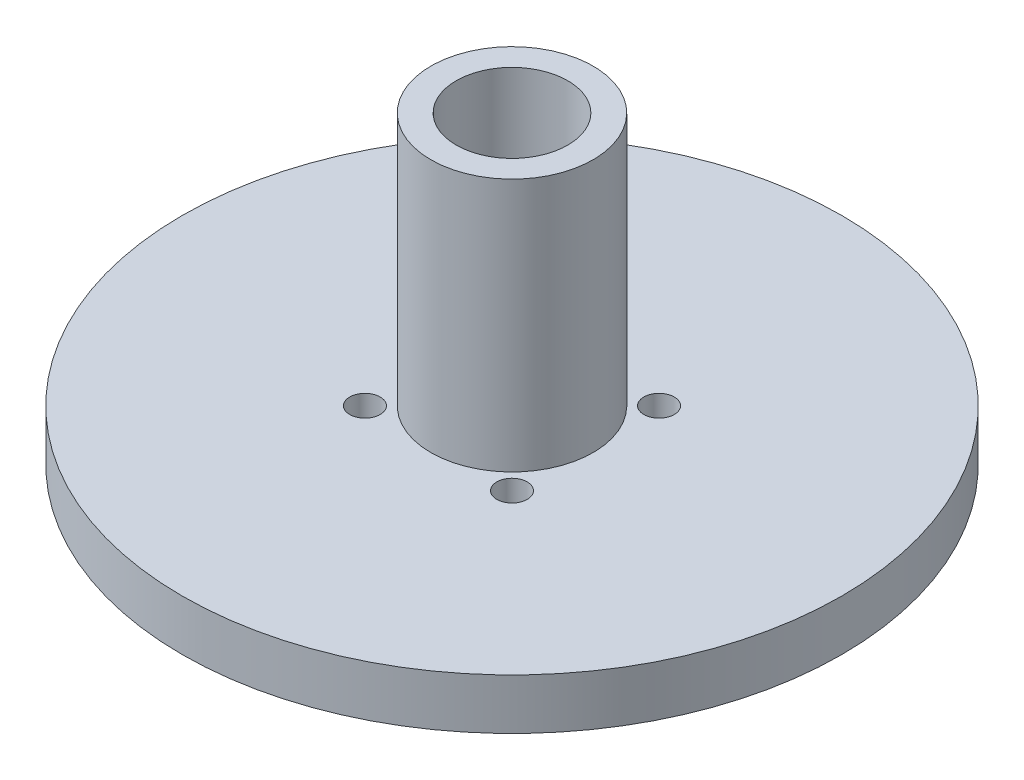
SolidWorks part; units mm, degrees
material "Ceramic Porcelain"
ref_plane "Front Plane" through (0, 0, 0) normal (0, 0, 1) x (1, 0, 0)
ref_plane "Top Plane" through (0, 0, 0) normal (0, 1, 0) x (1, 0, 0)
ref_plane "Right Plane" through (0, 0, 0) normal (1, 0, 0) x (0, 0, -1)
sketch "Sketch1" plane through (0, 0, 0) normal (0, 1, 0) x (1, 0, 0)
  circle A0 centre (0, 0) radius 32.5
  circle A1 centre (0, 0) radius 8
  circle A2 centre (0, 0) radius 12.5
  circle A3 centre (0, 0) radius 17.5
  dimension "D1" = 65
  dimension "D2" = 16
  dimension "D3" = 25
  dimension "D4" = 35
extrude "Boss-Extrude1" add sketch "Sketch1" along normal blind 5 contours A0 A3 | A3 A2 | A2 A1
sketch "Sketch2" plane through (0, 0, 0) normal (0, 1, 0) x (1, 0, 0)
  line L0 (0, 0) -> (0, 12.5) construction
  line L1 (0, 0) -> (-8.8388, 8.8388) construction
  line L2 (0, 0) -> (-8.8388, -8.8388) construction
  circle A0 centre (0, 0) radius 10.25 construction
  circle A1 centre (0, 0) radius 12.5 construction
  circle A2 centre (-7.2478, 7.2478) radius 1.5
  circle A3 centre (7.2478, 7.2478) radius 1.5
  circle A4 centre (7.2478, -7.2478) radius 1.5
  circle A5 centre (-7.2478, -7.2478) radius 1.5
  point P9 (0, 0)
  point P18 (0, 0)
  dimension "D1" = 20.5
  dimension "D2" = 25
  dimension "D4" = 3
  dimension "D3" = 45
  dimension "D6" = 45
  dimension "D5" = 4
extrude "Cut-Extrude1" cut sketch "Sketch2" along normal blind 10
sketch "Sketch3" plane through (0, 0, 0) normal (0, 1, 0) x (1, 0, 0)
  circle A0 centre (0, 0) radius 8
  circle A1 centre (0, 0) radius 5.5
  dimension "D1" = 16
  dimension "D2" = 11
extrude "Boss-Extrude3" add sketch "Sketch3" along normal blind 30
